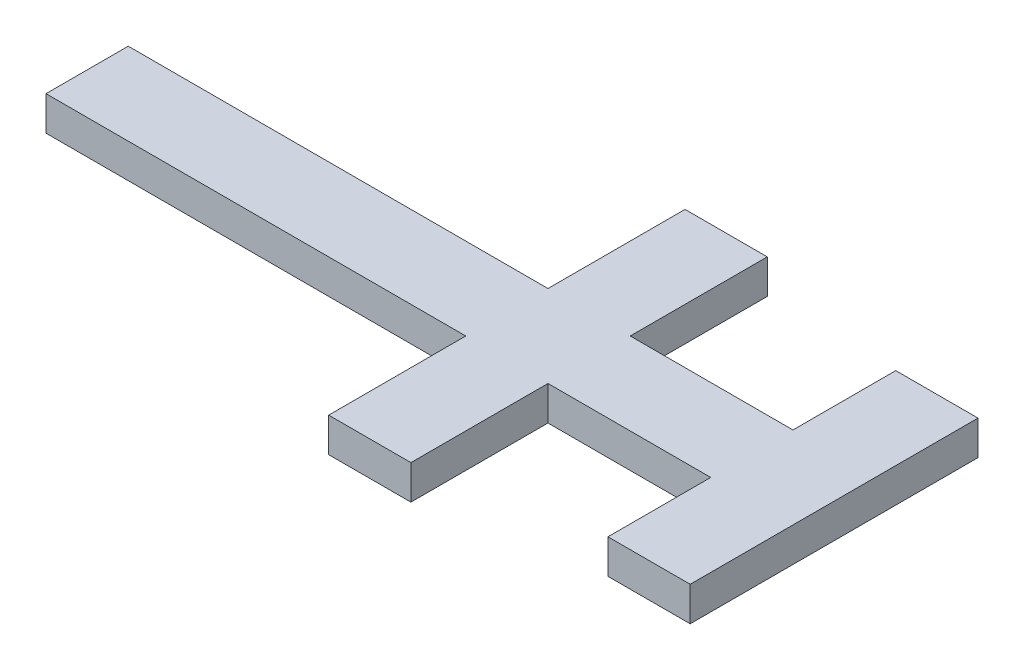
SolidWorks part; units mm, degrees
ref_plane "前视基准面" through (0, 0, 0) normal (0, 0, 1) x (1, 0, 0)
ref_plane "上视基准面" through (0, 0, 0) normal (0, 1, 0) x (1, 0, 0)
ref_plane "右视基准面" through (0, 0, 0) normal (1, 0, 0) x (0, 0, -1)
other "Configuration Table"
sketch "草图2" plane through (0, 0, 0) normal (0, 1, 0) x (1, 0, 0)
  line L0 (0, 0) -> (-37, 0) construction
  line L5 (-15, -5) -> (15, -5)
  line L6 (-15, -5) -> (-15, 5)
  line L7 (-15, 5) -> (15, 5)
  line L8 (15, -5) -> (15, 5)
  line L9 (-15, -5) -> (15, 5) construction
  line L10 (-15, 5) -> (15, -5) construction
  line L11 (20, 0) -> (15, 0) construction
  line L12 (-17, -5) -> (-57, -5)
  line L13 (-17, -5) -> (-17, 5)
  line L14 (-17, 5) -> (-57, 5)
  line L15 (-57, -5) -> (-57, 5)
  line L16 (-17, -5) -> (-57, 5) construction
  line L17 (-17, 5) -> (-57, -5) construction
  line L18 (-10.75, -25) -> (-20.75, -25)
  line L19 (-10.75, -25) -> (-10.75, 25)
  line L20 (-10.75, 25) -> (-20.75, 25)
  line L21 (-20.75, -25) -> (-20.75, 25)
  line L22 (-10.75, -25) -> (-20.75, 25) construction
  line L23 (-10.75, 25) -> (-20.75, -25) construction
  line L24 (25, -20) -> (15, -20)
  line L25 (25, -20) -> (25, 20)
  line L26 (25, 20) -> (15, 20)
  line L27 (15, -20) -> (15, 20)
  line L28 (25, -20) -> (15, 20) construction
  line L29 (25, 20) -> (15, -20) construction
  line L31 (-57, 5) -> (-82, 5)
  line L32 (-57, 5) -> (-57, -5)
  line L33 (-57, -5) -> (-82, -5)
  line L34 (-82, 5) -> (-82, -5)
  point P0 (0, 0)
  point P13 (20, 0)
  point P15 (-15.75, 0)
  dimension "D1" = 10
  dimension "D2" = 30
  dimension "D3" = 40
  dimension "D4" = 10
  dimension "D5" = 37
  dimension "D6" = 10
  dimension "D7" = 0.75
  dimension "D8" = 50
  dimension "D9" = 10
  dimension "D10" = 5
  dimension "D11" = 40
  dimension "D12" = 25
sketch "草图3" plane through (0, 0, 0) normal (0, 1, 0) x (1, 0, 0)
  line L0 (-15, -5) -> (15, -5) construction
  line L1 (25, 20) -> (15, 20)
  line L2 (25, 20) -> (25, -20)
  line L3 (25, -20) -> (15, -20)
  line L4 (15, 20) -> (15, -20)
  line L5 (15, 5) -> (-10.75, 5)
  line L6 (15, 5) -> (15, -5)
  line L7 (15, -5) -> (-10.75, -5)
  line L8 (-10.75, 5) -> (-10.75, -5)
  line L9 (-10.75, -25) -> (-10.75, 25) construction
  line L10 (-17, 5) -> (-57, 5) construction
  line L11 (-10.75, 25) -> (-20.75, 25)
  line L12 (-10.75, 25) -> (-10.75, -25)
  line L13 (-10.75, -25) -> (-20.75, -25)
  line L14 (-20.75, 25) -> (-20.75, -25)
  line L15 (-57, -5) -> (-20.75, -5)
  line L16 (-57, -5) -> (-57, 5)
  line L17 (-57, 5) -> (-20.75, 5)
  line L18 (-20.75, -5) -> (-20.75, 5)
  line L20 (-57, 5) -> (-82, 5)
  line L21 (-57, 5) -> (-57, -5)
  line L22 (-57, -5) -> (-82, -5)
  line L23 (-82, 5) -> (-82, -5)
extrude "凸台-拉伸1" add sketch "草图3" along normal blind 1 contours L1 L4 L3 L2 | L5 L8 L7 L4 | L11 L14 L13 L12 L8 | L17 L16 L15 L14 | L20 L23 L22 L16
sketch "草图4" plane through (0, 0, 0) normal (0, -1, 0) x (1, 0, 0)
  line L0 (14, -21) -> (26, -21)
  line L1 (26, -21) -> (26, 21)
  line L2 (26, 21) -> (14, 21)
  line L3 (14, 21) -> (14, 6)
  line L4 (14, 6) -> (-9.75, 6)
  line L5 (-9.75, 6) -> (-9.75, 26)
  line L6 (-9.75, 26) -> (-21.75, 26)
  line L7 (-21.75, 26) -> (-21.75, 6)
  line L8 (-21.75, 6) -> (-83, 6)
  line L9 (-83, 6) -> (-83, -6)
  line L10 (-83, -6) -> (-21.75, -6)
  line L11 (-21.75, -6) -> (-21.75, -26)
  line L12 (-21.75, -26) -> (-9.75, -26)
  line L13 (-9.75, -26) -> (-9.75, -6)
  line L14 (-9.75, -6) -> (14, -6)
  line L15 (14, -6) -> (14, -21)
  line L16 (15, -20) -> (25, -20)
  line L17 (25, -20) -> (25, 20)
  line L18 (25, 20) -> (15, 20)
  line L19 (15, 20) -> (15, 5)
  line L20 (15, 5) -> (-10.75, 5)
  line L21 (-10.75, 5) -> (-10.75, 25)
  line L22 (-10.75, 25) -> (-20.75, 25)
  line L23 (-20.75, 25) -> (-20.75, 5)
  line L24 (-20.75, 5) -> (-82, 5)
  line L25 (-82, 5) -> (-82, -5)
  line L26 (-82, -5) -> (-20.75, -5)
  line L27 (-20.75, -5) -> (-20.75, -25)
  line L28 (-20.75, -25) -> (-10.75, -25)
  line L29 (-10.75, -25) -> (-10.75, -5)
  line L30 (-10.75, -5) -> (15, -5)
  line L31 (15, -5) -> (15, -20)
  line L32 (15, -20) -> (25, -20)
  line L33 (25, -20) -> (25, 20)
  line L34 (25, 20) -> (15, 20)
  line L35 (15, 20) -> (15, 5)
  line L36 (15, 5) -> (-10.75, 5)
  line L37 (-10.75, 5) -> (-10.75, 25)
  line L38 (-10.75, 25) -> (-20.75, 25)
  line L39 (-20.75, 25) -> (-20.75, 5)
  line L40 (-20.75, 5) -> (-82, 5)
  line L41 (-82, 5) -> (-82, -5)
  line L42 (-82, -5) -> (-20.75, -5)
  line L43 (-20.75, -5) -> (-20.75, -25)
  line L44 (-20.75, -25) -> (-10.75, -25)
  line L45 (-10.75, -25) -> (-10.75, -5)
  line L46 (-10.75, -5) -> (15, -5)
  line L47 (15, -5) -> (15, -20)
  dimension "D1" = 0
  dimension "D2" = 1
extrude "凸台-拉伸2" add sketch "草图4" along normal blind 4 and the other way blind 1
sketch "草图5" plane through (0, 0, 0) normal (0, -1, 0) x (1, 0, 0)
  line L0 (-20.75, 25) -> (-20.75, 5)
  line L1 (-82, 5) -> (-57, 5)
  line L2 (-82, 5) -> (-82, -5)
  line L3 (-82, -5) -> (-57, -5)
  line L4 (-57, 5) -> (-57, -5)
  line L5 (15, 20) -> (25, 20)
  line L6 (15, 20) -> (15, -20)
  line L7 (15, -20) -> (25, -20)
  line L8 (25, 20) -> (25, -20)
  line L9 (-20.75, 5) -> (-17, 5)
  line L10 (-17, 5) -> (-17, -5)
  line L11 (-17, -5) -> (-20.75, -5)
  line L12 (-20.75, -5) -> (-20.75, -25)
  line L13 (-20.75, -25) -> (-10.75, -25)
  line L14 (-10.75, -25) -> (-10.75, -5)
  line L15 (-10.75, -5) -> (-15, -5)
  line L16 (-15, -5) -> (-15, 5)
  line L17 (-15, 5) -> (-10.75, 5)
  line L18 (-10.75, 5) -> (-10.75, 25)
  line L19 (-10.75, 25) -> (-20.75, 25)
extrude "凸台-拉伸3" add sketch "草图5" along normal blind 2
